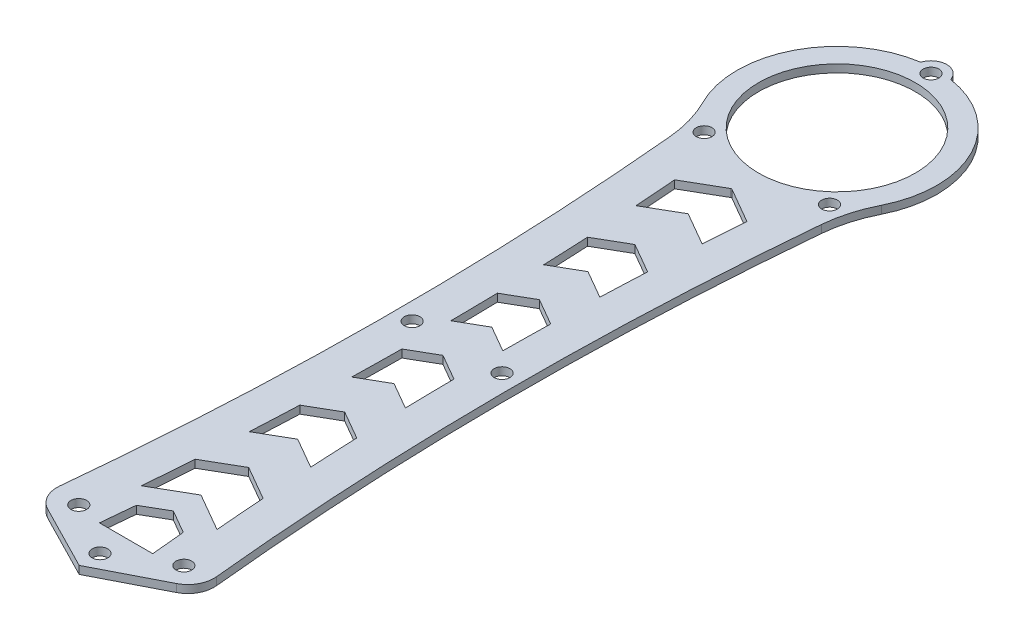
SolidWorks part; units mm, degrees
ref_plane "前基準面" through (0, 0, 0) normal (0, 0, 1) x (1, 0, 0)
ref_plane "上基準面" through (0, 0, 0) normal (0, 1, 0) x (1, 0, 0)
ref_plane "右基準面" through (0, 0, 0) normal (1, 0, 0) x (0, 0, -1)
sketch "草圖1" plane through (0, 0, 0) normal (0, 1, 0) x (1, 0, 0)
  line L0 (-45.7929, 39.3947) -> (118.2116, 38.9653) construction
  line L1 (0, -25.4446) -> (0, 154.6519) construction
  line L2 (0, 14.0424) -> (-4.4911, 11.4495)
  line L3 (0, -3.9809) -> (12.3191, 2.3288)
  line L4 (0, 112.5321) -> (-6.334, 108.8752)
  line L5 (0, 112.5321) -> (6.334, 108.8752)
  line L6 (-46.5392, 127.5836) -> (-7.6665, 127.5836) construction
  line L7 (0, 102.3449) -> (5.754, 99.0229)
  line L8 (0.1364, 120.7804) -> (6.9215, 116.863)
  line L9 (0, 84.0727) -> (5.1071, 81.1241)
  line L10 (0, 74.9698) -> (4.9796, 72.0949)
  line L11 (0, 65.6198) -> (4.9879, 62.74)
  line L12 (0, 93.3641) -> (5.3719, 90.2626)
  line L13 (0, 56.2626) -> (5.1412, 53.2943)
  line L14 (0, 46.8277) -> (5.447, 43.6829)
  line L15 (0, 37.8313) -> (5.884, 34.4342)
  line L16 (0, 28.4608) -> (6.4948, 24.7111)
  line L17 (0, 19.3311) -> (7.2473, 15.1468)
  line L18 (0, 14.0424) -> (4.4911, 11.4495)
  line L19 (-5.1012, 5.0028) -> (5.1012, 5.0028)
  line L20 (0, 19.3311) -> (-7.2473, 15.1468)
  line L21 (0, 28.4608) -> (-6.4948, 24.7111)
  line L22 (0, 37.8313) -> (-5.884, 34.4342)
  line L23 (0, 46.8277) -> (-5.447, 43.6829)
  line L24 (0, 56.2626) -> (-5.1412, 53.2943)
  line L25 (0, 65.6198) -> (-4.9879, 62.74)
  line L26 (0, 74.9698) -> (-4.9796, 72.0949)
  line L27 (0, 84.0727) -> (-5.1071, 81.1241)
  line L28 (0, 93.3641) -> (-5.3719, 90.2626)
  line L29 (0, 102.3449) -> (-5.754, 99.0229)
  line L30 (-4.4911, 11.4495) -> (-5.1012, 5.0028)
  line L31 (-0.1364, 120.7804) -> (-6.9215, 116.863)
  line L32 (0, -3.9809) -> (-12.3191, 2.3288)
  line L33 (4.4911, 11.4495) -> (5.1012, 5.0028)
  line L36 (0, 3.8839) -> (-7.9144, 7.9376) construction
  line L37 (0, 3.8839) -> (7.9144, 7.9376) construction
  circle A1 centre (-12, 127.5836) radius 1.5
  circle A2 centre (12, 127.5836) radius 1.5
  circle A3 centre (8.6, 68.3254) radius 1.5
  circle A4 centre (-8.6, 68.3254) radius 1.5
  circle A5 centre (10.05, 6) radius 1.5
  circle A6 centre (-10.05, 6) radius 1.5
  circle A7 centre (0, 159) radius 1.5
  circle A8 centre (0, 0) radius 1.5
  circle A9 centre (0, 141) radius 15
  arc A10 (7.5514, 124.1751) -> (7.9144, 7.9376) centre (617.3178, 67.9598) ccw construction
  arc A11 (-5.754, 99.0229) -> (-5.3719, 90.2626) centre (-617.3178, 67.9598) cw
  arc A12 (5.754, 99.0229) -> (5.3719, 90.2626) centre (617.3178, 67.9598) ccw
  arc A13 (-12.3191, 2.3288) -> (-15.0145, 7.2803) centre (-10.0397, 6.7791) cw
  arc A14 (0.1364, 120.7804) -> (-0.1364, 120.7804) centre (0, 120.5442) ccw
  arc A15 (14.5218, 123.5325) -> (15.0145, 7.2803) centre (617.3178, 67.9598) ccw
  arc A16 (17.067, 132.4252) -> (2.8669, 159.8836) centre (0, 141) ccw
  arc A17 (12.3191, 2.3288) -> (15.0145, 7.2803) centre (10.0397, 6.7791) ccw
  arc A18 (14.5218, 123.5325) -> (17.067, 132.4252) centre (39.3167, 121.2466) cw
  arc A19 (-14.5218, 123.5325) -> (-17.067, 132.4252) centre (-39.3167, 121.2466) ccw
  arc A20 (6.9215, 116.863) -> (6.334, 108.8752) centre (617.3178, 67.9598) ccw
  arc A21 (-14.5218, 123.5325) -> (-15.0145, 7.2803) centre (-617.3178, 67.9598) cw
  arc A22 (7.9144, 7.9376) -> (7.9144, 7.9376) centre (7.9144, 7.9376) ccw
  arc A23 (-7.9144, 7.9376) -> (-7.9144, 7.9376) centre (-7.9144, 7.9376) cw
  arc A24 (-6.9215, 116.863) -> (-6.334, 108.8752) centre (-617.3178, 67.9598) cw
  arc A25 (-7.5514, 124.1751) -> (-7.9144, 7.9376) centre (-617.3178, 67.9598) cw construction
  arc A26 (5.1071, 81.1241) -> (4.9796, 72.0949) centre (617.3178, 67.9598) ccw
  arc A27 (-5.1071, 81.1241) -> (-4.9796, 72.0949) centre (-617.3178, 67.9598) cw
  arc A28 (10.8121, 135.5678) -> (-10.8121, 135.5678) centre (0, 141) ccw construction
  arc A29 (-7.5514, 124.1751) -> (-10.8121, 135.5678) centre (-39.3167, 121.2466) ccw construction
  arc A30 (7.5514, 124.1751) -> (10.8121, 135.5678) centre (39.3167, 121.2466) cw construction
  arc A31 (-4.9879, 62.74) -> (-5.1412, 53.2943) centre (-617.3178, 67.9598) cw
  arc A32 (4.9879, 62.74) -> (5.1412, 53.2943) centre (617.3178, 67.9598) ccw
  arc A33 (-5.447, 43.6829) -> (-5.884, 34.4342) centre (-617.3178, 67.9598) cw
  arc A34 (5.447, 43.6829) -> (5.884, 34.4342) centre (617.3178, 67.9598) ccw
  arc A35 (-6.4948, 24.7111) -> (-7.2473, 15.1468) centre (-617.3178, 67.9598) cw
  arc A36 (6.4948, 24.7111) -> (7.2473, 15.1468) centre (617.3178, 67.9598) ccw
  arc A37 (2.8669, 159.8836) -> (-2.8669, 159.8836) centre (0, 159) ccw
  circle A38 centre (0, 159) radius 3 construction
  arc A39 (-2.8669, 159.8836) -> (-17.067, 132.4252) centre (0, 141) ccw
  arc A40 (17.067, 132.4252) -> (-17.067, 132.4252) centre (0, 141) ccw construction
  point P3 (12, 127.567)
  point P23 (-0.1364, 126)
  point P26 (0, 141)
  point P42 (0, 115.0816)
  point P77 (0, 5.0028)
  dimension "D3" = 3
  dimension "D4" = 3
  dimension "D5" = 3
  dimension "D6" = 3
  dimension "D7" = 3
  dimension "D8" = 7
  dimension "D9" = 141
  dimension "D10" = 5
  dimension "D11" = 24
  dimension "D12" = 120
  dimension "D13" = 0.2728
  dimension "D14" = 38.2
  dimension "D15" = 20.1
  dimension "D16" = 24.9
  dimension "D22" = 30
  dimension "D17" = 6
  dimension "D18" = 17.2
  dimension "D20" = 18
  dimension "D21" = 18
  dimension "D19" = 1.5
extrude "填料-伸長1" add sketch "草圖1" along normal blind 1.5 contours A19 A21 A13 L32 L3 A17 A15 A18 A16 A7 A27 L27 L9 A26 L10 L26 A24 L31 A14 L8 A20 L5 L4 L7 A12 L12 L28 A11 L29 A6 A5 A2 A1 L18 L33 L19 L30 L2 A3 A4
